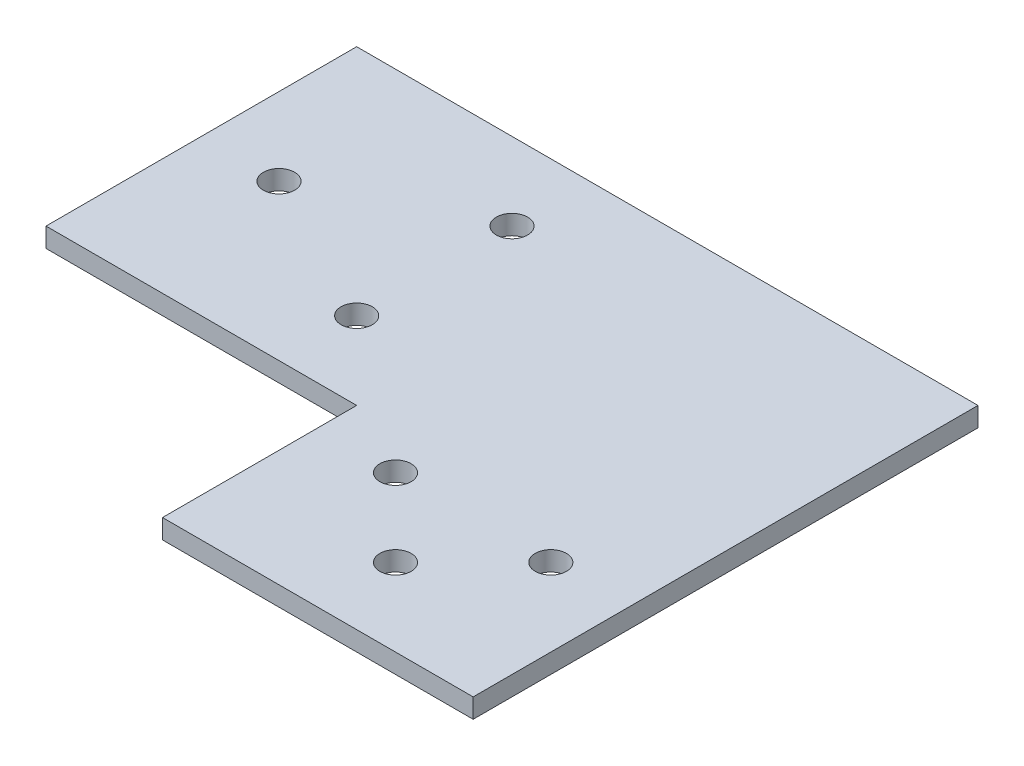
SolidWorks part; units mm, degrees
ref_plane "Front Plane" through (0, 0, 0) normal (0, 0, 1) x (1, 0, 0)
ref_plane "Top Plane" through (0, 0, 0) normal (0, 1, 0) x (1, 0, 0)
ref_plane "Right Plane" through (0, 0, 0) normal (1, 0, 0) x (0, 0, -1)
sketch "Sketch1" plane through (0, 0, 0) normal (0, 1, 0) x (1, 0, 0)
  line L1 (0, 0) -> (50.8, 0)
  line L2 (0, 0) -> (0, 50.8)
  line L3 (0, 50.8) -> (101.6, 50.8)
  line L4 (50.8, -31.75) -> (101.6, -31.75)
  line L6 (50.8, 0) -> (50.8, -31.75)
  line L8 (101.6, 50.8) -> (101.6, -31.75)
  line L10 (38.1, 38.1) -> (38.1, 12.7) construction
  circle A0 centre (12.7, 25.4) radius 2.5527
  circle A1 centre (38.1, 12.7) radius 2.5527
  circle A2 centre (38.1, 38.1) radius 2.5527
  circle A6 centre (63.5, -6.35) radius 2.5527
  circle A7 centre (88.9, -6.35) radius 2.5527
  circle A8 centre (76.2, -19.05) radius 2.5527
  point P23 (0, 25.4)
  point P26 (38.1, 25.4)
  dimension "D5" = 5.1054
  dimension "D17" = 5.1054
  dimension "D18" = 12.7
  dimension "D2" = 50.8
  dimension "D3" = 12.7
  dimension "D4" = 50.8
  dimension "D6" = 12.7
  dimension "D7" = 25.4
  dimension "D9" = 38.1
  dimension "D12" = 50.8
  dimension "D15" = 57.15
  dimension "D16" = 69.85
  dimension "D19" = 25.4
  dimension "D20" = 38.1
extrude "Boss-Extrude1" add sketch "Sketch1" along normal blind 3.175
